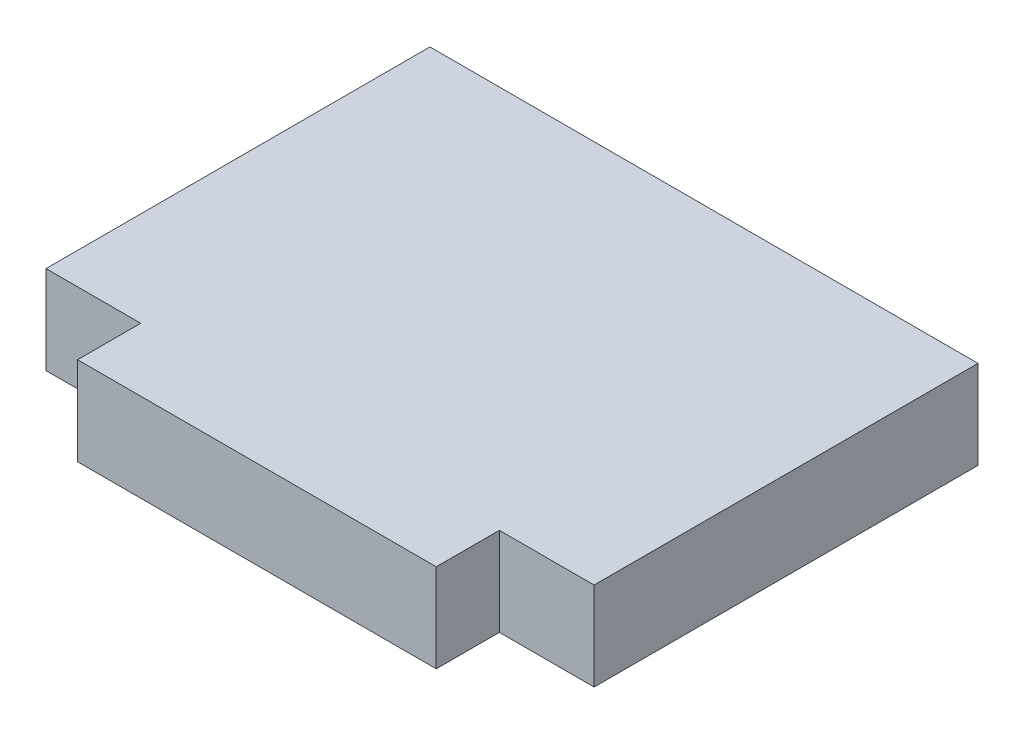
SolidWorks part; units mm, degrees
ref_plane "Front Plane" through (0, 0, 0) normal (0, 0, 1) x (1, 0, 0)
ref_plane "Top Plane" through (0, 0, 0) normal (0, 1, 0) x (1, 0, 0)
ref_plane "Right Plane" through (0, 0, 0) normal (1, 0, 0) x (0, 0, -1)
sketch "Sketch1" plane through (0, 0, 0) normal (0, 1, 0) x (1, 0, 0)
  line L1 (-55.118, 25.2861) -> (55.118, 25.2861)
  line L2 (-55.118, 25.2861) -> (-55.118, -64.6299)
  line L3 (-55.118, -64.6299) -> (55.118, -64.6299)
  line L4 (55.118, 25.2861) -> (55.118, -64.6299)
  line L5 (-55.118, 25.2861) -> (55.118, -64.6299) construction
  line L6 (-55.118, -64.6299) -> (55.118, 25.2861) construction
  point P0 (0, -19.6719)
  dimension "D1" = 110.236
  dimension "D2" = 89.916
extrude "Boss-Extrude1" add sketch "Sketch1" along normal blind 17.78
sketch "Sketch2" plane through (0, 17.78, 0) normal (0, 1, 0) x (1, 0, 0)
  line L1 (-55.118, -64.6299) -> (-36.068, -64.6299)
  line L2 (-55.118, -64.6299) -> (-55.118, -51.9299)
  line L3 (-55.118, -51.9299) -> (-36.068, -51.9299)
  line L4 (-36.068, -64.6299) -> (-36.068, -51.9299)
  line L5 (55.118, -64.6299) -> (36.068, -64.6299)
  line L6 (55.118, -64.6299) -> (55.118, -51.9299)
  line L7 (55.118, -51.9299) -> (36.068, -51.9299)
  line L8 (36.068, -64.6299) -> (36.068, -51.9299)
  dimension "D1" = 12.7
  dimension "D2" = 12.7
  dimension "D3" = 19.05
  dimension "D4" = 19.05
extrude "Cut-Extrude1" cut sketch "Sketch2" against normal blind 17.78
